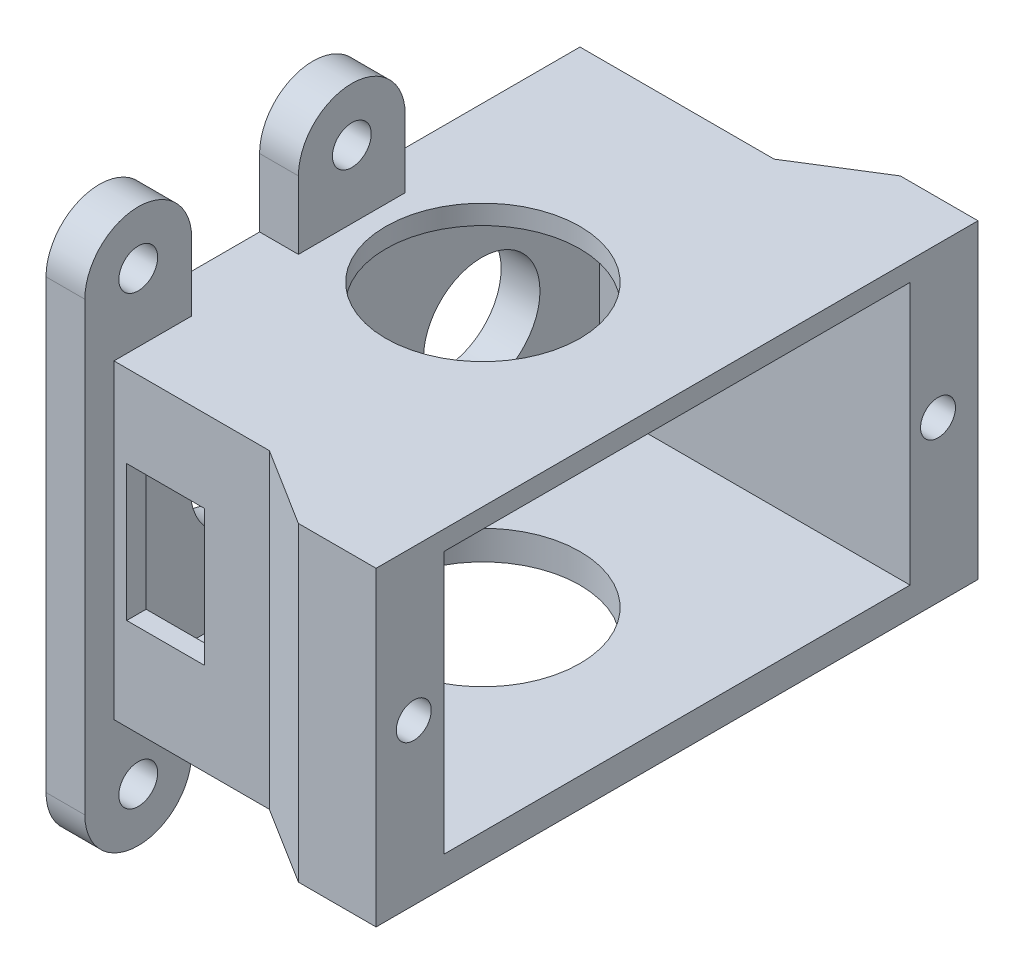
SolidWorks part; units mm, degrees
material "uhlíková ocel 7850"
ref_plane "Přední rovina" through (0, 0, 0) normal (0, 0, 1) x (1, 0, 0)
ref_plane "Horní rovina" through (0, 0, 0) normal (0, 1, 0) x (1, 0, 0)
ref_plane "Pravá rovina" through (0, 0, 0) normal (1, 0, 0) x (0, 0, -1)
sketch "Skica1" plane through (0, 0, 0) normal (0, 1, 0) x (1, 0, 0)
  line L0 (0, -11) -> (0, 11)
  line L1 (0, 11) -> (-3.25, 14.25)
  line L2 (-3.25, 14.25) -> (-30.25, 14.25)
  line L3 (-30.25, 14.25) -> (-30.25, 16.25)
  line L4 (-30.25, 16.25) -> (-2.4216, 16.25)
  line L5 (-2.4216, 16.25) -> (2, 11.8284)
  line L6 (2, 11.8284) -> (2, -11.8284)
  line L7 (2, 0) -> (0, 0) construction
  line L8 (-2.4216, -16.25) -> (2, -11.8284)
  line L9 (-30.25, -16.25) -> (-2.4216, -16.25)
  line L10 (-30.25, -14.25) -> (-30.25, -16.25)
  line L11 (-3.25, -14.25) -> (-30.25, -14.25)
  line L12 (0, -11) -> (-3.25, -14.25)
  dimension "D1" = 11
  dimension "D2" = 135
  dimension "D3" = 27
  dimension "D4" = 2
  dimension "D5" = 2
  dimension "D6" = 2
  dimension "D7" = 14.25
extrude "Přidat vysunutím1" add sketch "Skica1" along normal blind 15
sketch "Skica8" plane through (0, 0, 0) normal (0, -1, 0) x (1, 0, 0)
  line L0 (-2.4216, 16.25) -> (2, 11.8284) construction
  line L1 (-0.3431, 14.1716) -> (26, 14.1716)
  line L2 (2, -11.8284) -> (2, 11.8284)
  line L3 (2, -11.8284) -> (26, -11.8284)
  line L4 (26, 14.1716) -> (26, -11.8284)
  line L5 (2, 11.8284) -> (-0.3431, 14.1716)
  line L6 (0, -11) -> (0, 11) construction
  line L7 (2, -11.8284) -> (-2.4216, -16.25) construction
  dimension "D1" = 26
  dimension "D2" = 26
extrude "Přidat vysunutím2" add sketch "Skica8" against normal up to surface (15 mm away) up to face at (-10.6953, 15, 0)
sketch "Skica10" plane through (0, 15, 0) normal (0, 1, 0) x (1, 0, 0)
  line L0 (26, -14.1716) -> (26, 11.8284) construction
  line L1 (26, 10.8284) -> (10, 10.8284)
  line L2 (26, 10.8284) -> (26, -13.1716)
  line L3 (26, -13.1716) -> (10, -13.1716)
  line L4 (10, 10.8284) -> (10, -13.1716)
  line L6 (-0.3431, -14.1716) -> (26, -14.1716) construction
  dimension "D1" = 24
  dimension "D2" = 1
  dimension "D3" = 16
extrude "Odebrat vysunutím7" cut sketch "Skica10" against normal blind 13.5
sketch "Skica11" plane through (26, 0, 0) normal (1, 0, 0) x (0, 0, -1)
  line L0 (-16.25, 0) -> (-14.1716, 0) construction
  line L1 (-14.1716, 15) -> (-16.6716, 15)
  line L2 (-14.1716, 15) -> (-14.1716, 0)
  line L3 (-14.1716, 0) -> (-16.6716, 0)
  line L4 (-16.6716, 15) -> (-16.6716, 0)
  line L5 (11.8284, 0) -> (16.25, 0) construction
  line L6 (11.8284, 15) -> (14.3284, 15)
  line L7 (11.8284, 15) -> (11.8284, 0)
  line L8 (11.8284, 0) -> (14.3284, 0)
  line L9 (14.3284, 15) -> (14.3284, 0)
  dimension "D1" = 2.5
extrude "Přidat vysunutím3" add sketch "Skica11" against normal blind 4
sketch "Skica12" plane through (26, 0, 0) normal (1, 0, 0) x (0, 0, -1)
  line L0 (-14.7302, 8.25) -> (12.2698, 8.25) construction
  line L1 (-14.7302, 8.25) -> (-13.1716, 8.25) construction
  line L2 (-13.1716, 1.5) -> (-13.1716, 15) construction
  circle A0 centre (-14.7302, 8.25) radius 0.9
  circle A1 centre (12.2698, 8.25) radius 0.9
  dimension "D1" = 1.8
  dimension "D2" = 27
extrude "Odebrat vysunutím8" cut sketch "Skica12" against normal blind 4
sketch "Skica13" plane through (0, 0, 14.1716) normal (0, 0, 1) x (1, 0, 0)
  line L1 (10.6569, 11.75) -> (14.6569, 11.75)
  line L2 (10.6569, 11.75) -> (10.6569, 4.75)
  line L3 (10.6569, 4.75) -> (14.6569, 4.75)
  line L4 (14.6569, 11.75) -> (14.6569, 4.75)
  line L5 (-0.3431, 15) -> (-0.3431, 0) construction
  line L6 (22, 8.25) -> (14.6569, 8.25) construction
  line L7 (22, 7.5444) -> (22, 8.9556) construction
  dimension "D1" = 4
  dimension "D2" = 7
  dimension "D3" = 11
extrude "Odebrat vysunutím9" cut sketch "Skica13" against normal blind 4
sketch "Skica17" plane through (0, 15, 0) normal (0, 1, 0) x (1, 0, 0)
  line L0 (10, 10.8284) -> (10, -13.1716) construction
  line L1 (-30.25, 16.25) -> (8, 16.25)
  line L2 (-30.25, 16.25) -> (-30.25, -16.25)
  line L3 (-30.25, -16.25) -> (8, -16.25)
  line L4 (8, 16.25) -> (8, -16.25)
  dimension "D1" = 2
extrude "Odebrat vysunutím10" cut sketch "Skica17" against normal through all
sketch "Skica19" plane through (0, 15, 0) normal (0, 1, 0) x (1, 0, 0)
  line L0 (8, 11.8284) -> (22, 11.8284)
  line L1 (22, 11.8284) -> (22, 14.3284)
  line L2 (22, 14.3284) -> (26, 14.3284)
  line L3 (26, 14.3284) -> (26, -16.6716)
  line L4 (26, -16.6716) -> (22, -16.6716)
  line L5 (22, -16.6716) -> (22, -14.1716)
  line L6 (22, -14.1716) -> (8, -14.1716)
  line L7 (8, -14.1716) -> (8, 11.8284)
extrude "Přidat vysunutím4" add sketch "Skica19" along normal blind 1
sketch "Skica20" plane through (8, 0, 0) normal (-1, 0, 0) x (0, 0, 1)
  line L0 (-12.2698, 8.25) -> (14.7302, 8.25) construction
  line L1 (12.9216, -3.5) -> (12.9216, 19.5) construction
  line L2 (10.1716, -3.5) -> (10.1716, 0)
  line L3 (15.6716, -3.5) -> (15.6716, 0)
  line L4 (1.2302, 8.25) -> (1.2302, 16.8785) construction
  line L5 (10.1716, 16) -> (15.6716, 16)
  line L6 (-11.8284, 16) -> (14.1716, 16) construction
  line L7 (10.1716, 16) -> (10.1716, 19.5)
  line L8 (15.6716, 16) -> (15.6716, 19.5)
  line L9 (14.1716, 0) -> (-11.8284, 0) construction
  line L10 (15.6716, 0) -> (10.1716, 0)
  line L12 (-11.8284, 16) -> (-11.8284, 9.0344) construction
  arc A0 (10.1716, -3.5) -> (15.6716, -3.5) centre (12.9216, -3.5) ccw
  arc A1 (15.6716, 19.5) -> (10.1716, 19.5) centre (12.9216, 19.5) ccw
  circle A2 centre (12.9216, 19.5) radius 1
  circle A3 centre (12.9216, -3.5) radius 1
  point P6 (-6.36, 8.25)
  dimension "D3" = 2
  dimension "D1" = 24.75
  dimension "D2" = 5.5
  dimension "D4" = 23
  dimension "D5" = 22
extrude "Přidat vysunutím5" add sketch "Skica20" against normal blind 2
ref_plane "Rovina1" through (0, 0, 1.1716) normal (0, 0, -1) x (-1, 0, 0)
sketch "Skica21" plane through (0, 16, 0) normal (0, 1, 0) x (1, 0, 0)
  line L0 (6.6, -1.1716) -> (-6.6, -1.1716) construction
  line L1 (8, 11.8284) -> (8, -10.1716) construction
  circle A0 centre (16, -1.1716) radius 5
  dimension "D1" = 10
  dimension "D2" = 8
extrude "Odebrat vysunutím11" cut sketch "Skica21" against normal blind 22
pattern_linear "LinPole1" count 2 spacing 11 along (0, 0, -1) of "Přidat vysunutím5"
sketch "Skica22" plane through (10, 0, 0) normal (1, 0, 0) x (0, 0, -1)
  line L0 (-14.7302, 8.25) -> (12.2698, 8.25) construction
  line L1 (-1.2302, 8.25) -> (-1.1716, 15) construction
  line L2 (-13.1716, 15) -> (10.8284, 15) construction
  circle A0 centre (-7.2304, 8.25) radius 3
  circle A1 centre (4.7691, 8.1457) radius 3
  dimension "D1" = 6
  dimension "D2" = 6
extrude "Odebrat vysunutím12" cut sketch "Skica22" against normal blind 5
sketch "Skica23" plane through (0, 16, 0) normal (0, 1, 0) x (1, 0, 0)
  line L0 (22, 14.3284) -> (18, 11.8284)
  line L1 (22, 11.8284) -> (8, 11.8284) construction
  line L2 (18, 11.8284) -> (22, 11.8284)
  line L3 (22, 14.3284) -> (22, 11.8284) construction
  line L4 (22, 11.8284) -> (22, 14.3284)
  line L5 (22, -14.1716) -> (18, -14.1716)
  line L6 (10, -14.1716) -> (22, -14.1716) construction
  line L7 (18, -14.1716) -> (22, -16.6716)
  line L8 (22, -16.6716) -> (22, -14.1716)
  dimension "D1" = 4
extrude "Přidat vysunutím6" add sketch "Skica23" against normal up to surface (16 mm away) up to face at (15.2143, 0, 3.2609)
sketch "Skica24" plane through (0, 16, 0) normal (0, -1, 0) x (1, 0, 0)
  line L4 (8, 15.6716) -> (8, 14.1716)
  line L5 (8, 14.1716) -> (10, 14.1716)
  line L6 (10, 14.1716) -> (10, 15.6716)
  line L7 (10, 15.6716) -> (8, 15.6716)
  line L8 (8, 15.6716) -> (8, 14.1716)
  line L9 (8, 14.1716) -> (10, 14.1716)
  line L10 (10, 14.1716) -> (10, 15.6716)
  line L11 (10, 15.6716) -> (8, 15.6716)
  dimension "D1" = 0
extrude "Přidat vysunutím7" add sketch "Skica24" along normal up to surface (16 mm away) up to face at (9.25, 0, 15.1091)
